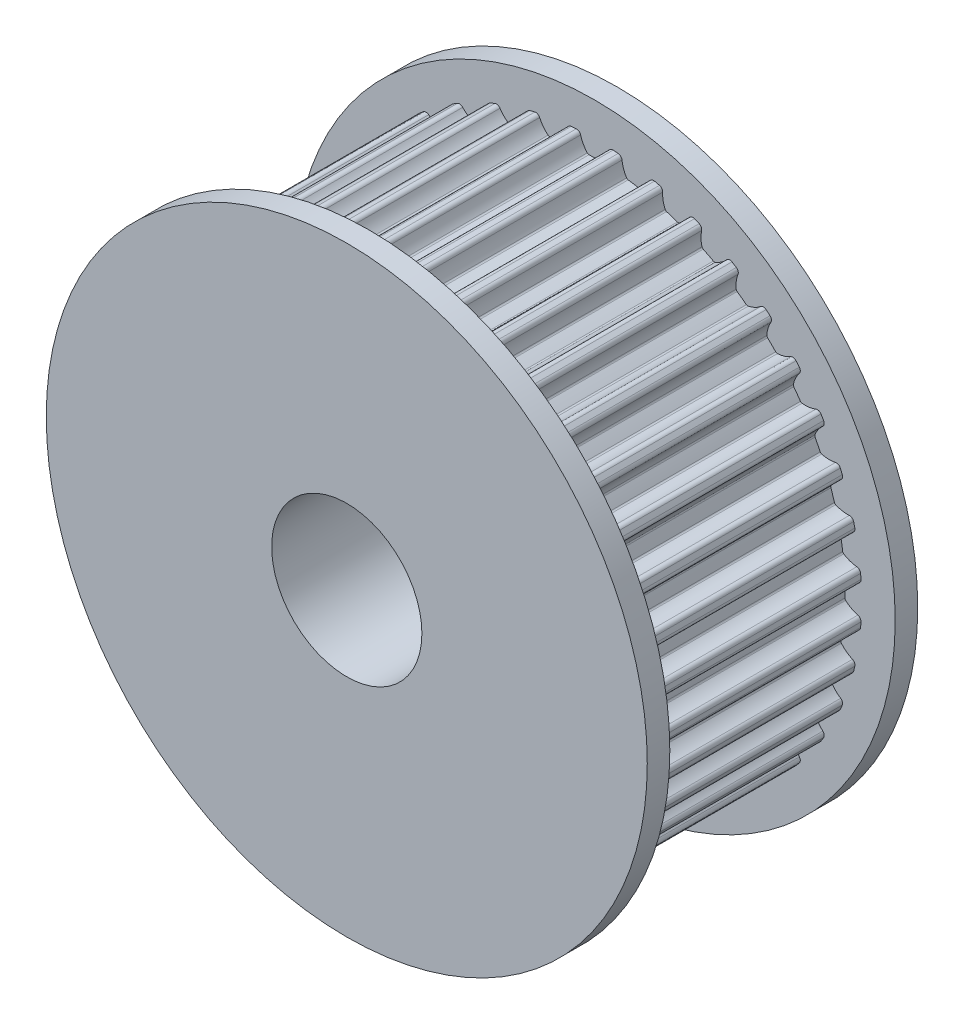
SolidWorks part; units mm, degrees
material "6061-T6 (SS)"
ref_plane "前基準面" through (0, 0, 0) normal (0, 0, 1) x (1, 0, 0)
ref_plane "上基準面" through (0, 0, 0) normal (0, 1, 0) x (1, 0, 0)
ref_plane "右基準面" through (0, 0, 0) normal (1, 0, 0) x (0, 0, -1)
sketch "草圖1" plane through (0, 0, 0) normal (0, 0, 1) x (1, 0, 0)
  circle A0 centre (0, 0) radius 17.765
  dimension "D1" = 35.53
extrude "填料-伸長1" add sketch "草圖1" along normal mid plane 15
sketch "草圖2" plane through (0, 0, 7.5) normal (0, 0, 1) x (1, 0, 0)
  line L0 (0, 0) -> (0, 17.765) construction
  line L1 (0, 17.765) -> (0, 18.019) construction
  line L2 (-0.975, 18.019) -> (0.975, 18.019) construction
  circle A0 centre (0, 0) radius 17.765 construction
  arc A1 (-0.3803, 16.6507) -> (0.3803, 16.6507) centre (0, 0) cw
  arc A2 (-0.3803, 16.6507) -> (-0.4954, 16.7005) centre (-0.3837, 16.8006) cw
  arc A3 (-0.4954, 16.7005) -> (-0.9346, 17.5149) centre (0.975, 18.019) cw
  arc A4 (-1.2246, 17.7227) -> (-0.9346, 17.5149) centre (-1.2053, 17.4434) cw
  arc A5 (0.3803, 16.6507) -> (0.4954, 16.7005) centre (0.3837, 16.8006) ccw
  arc A6 (0.4954, 16.7005) -> (0.9346, 17.5149) centre (-0.975, 18.019) ccw
  arc A7 (1.2246, 17.7227) -> (0.9346, 17.5149) centre (1.2053, 17.4434) ccw
  arc A8 (-1.2246, 17.7227) -> (1.2246, 17.7227) centre (0, 0) cw
  dimension "D1" = 0.15
  dimension "D2" = 1.975
  dimension "D3" = 0.28
  dimension "D4" = 1.11
  dimension "D5" = 0.254
  dimension "D6" = 1.95
extrude "除料-伸長1" cut sketch "草圖2" against normal through all and the other way through all
pattern_circular "環狀複製排列1" count 40 over 360 about axis through (0, 0, 0) along (0, 0, 1) of "除料-伸長1"
sketch "草圖3" plane through (0, 0, 7.5) normal (0, 0, 1) x (1, 0, 0)
  circle A0 centre (0, 0) radius 20
  dimension "D1" = 40
extrude "填料-伸長2" add sketch "草圖3" along normal blind 1.5
sketch "草圖9" plane through (0, 0, -7.5) normal (0, 0, -1) x (-1, 0, 0)
  circle A0 centre (0, 0) radius 20
  circle A1 centre (0, 0) radius 20 construction
extrude "填料-伸長3" add sketch "草圖9" along normal blind 1.5
sketch "草圖4" plane through (0, 0, 9) normal (0, 0, 1) x (1, 0, 0)
  circle A0 centre (0, 0) radius 5
  dimension "D1" = 10
extrude "除料-伸長2" cut sketch "草圖4" against normal through all
sketch "草圖10" plane through (0, 0, 0) normal (0, 1, 0) x (1, 0, 0)
  circle A0 centre (0, 0) radius 2
  dimension "D1" = 4
extrude "除料-伸長3" cut sketch "草圖10" against normal through all
sketch "草圖11" plane through (0, 0, 0) normal (1, 0, 0) x (0, 0, -1)
  circle A0 centre (0, 0) radius 2
  dimension "D1" = 4
extrude "除料-伸長4" cut sketch "草圖11" against normal through all
